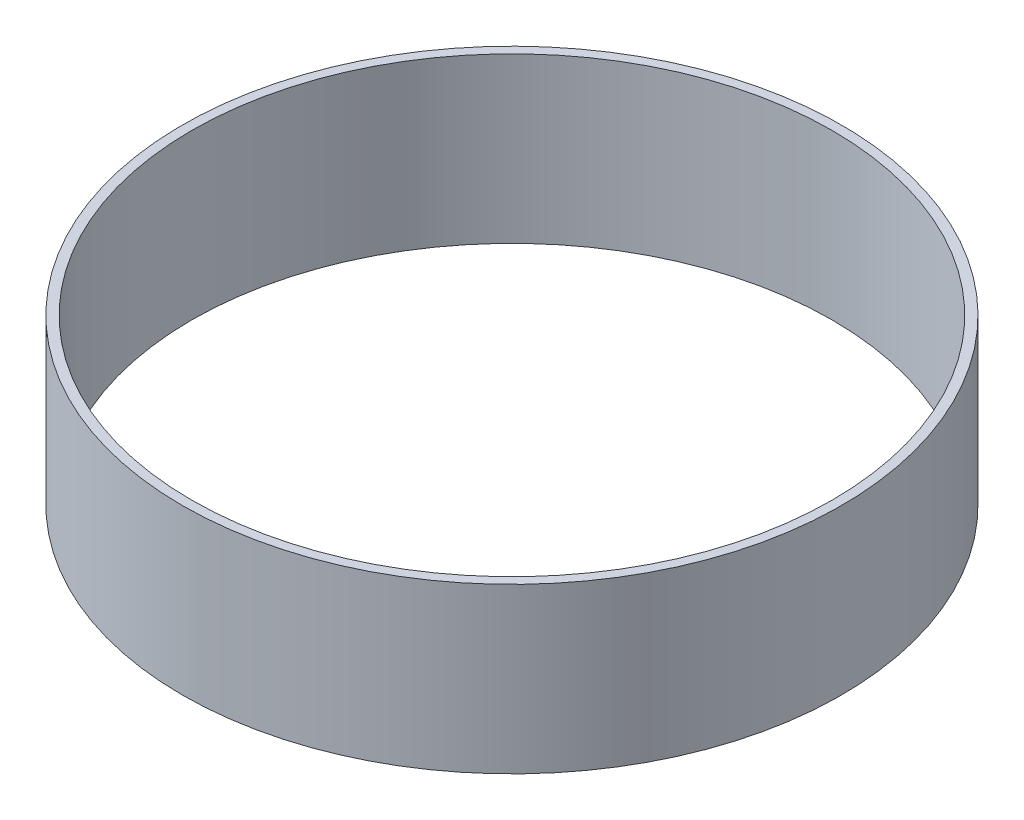
SolidWorks part; units mm, degrees
ref_plane "Front Plane" through (0, 0, 0) normal (0, 0, 1) x (1, 0, 0)
ref_plane "Top Plane" through (0, 0, 0) normal (0, 1, 0) x (1, 0, 0)
ref_plane "Right Plane" through (0, 0, 0) normal (1, 0, 0) x (0, 0, -1)
sketch "Sketch1" plane through (0, 0, 0) normal (0, 1, 0) x (1, 0, 0)
  circle A0 centre (0, 0) radius 51
  circle A1 centre (0, 0) radius 49.55
  dimension "D1" = 99.1
  dimension "D2" = 102
extrude "Boss-Extrude1" add sketch "Sketch1" along normal blind 25.4
